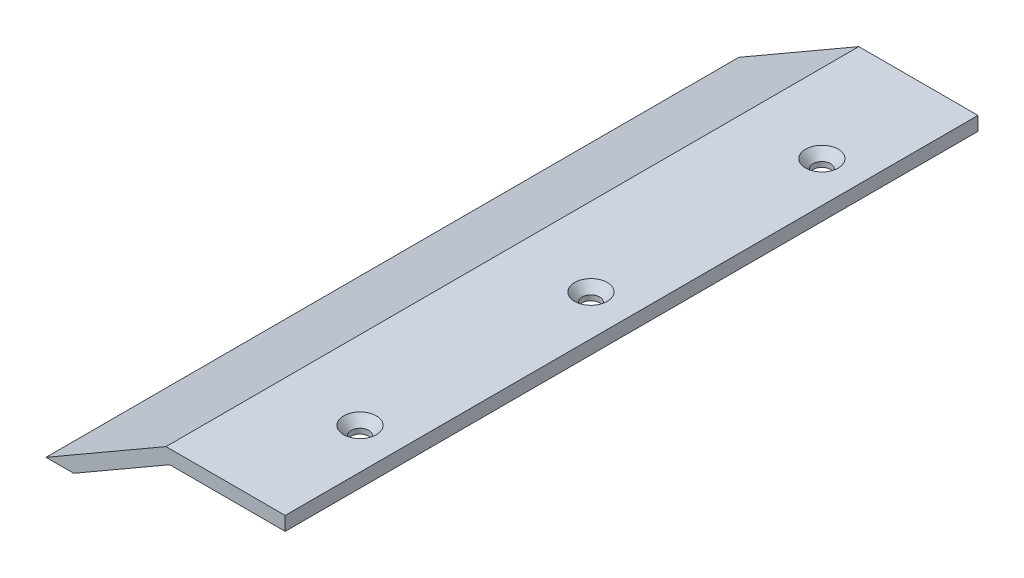
SolidWorks part; units mm, degrees
ref_plane "Alzado" through (0, 0, 0) normal (0, 0, 1) x (1, 0, 0)
ref_plane "Planta" through (0, 0, 0) normal (0, 1, 0) x (1, 0, 0)
ref_plane "Vista lateral" through (0, 0, 0) normal (1, 0, 0) x (0, 0, -1)
sketch "Croquis1" plane through (0, 0, 0) normal (0, 0, 1) x (1, 0, 0)
  line L1 (25, 0) -> (25, 3)
  line L2 (25, 3) -> (-0.8038, 3)
  line L3 (-0.8038, 3) -> (-26.7846, -12)
  line L4 (-26.7846, -12) -> (-20.7846, -12)
  line L5 (-20.7846, -12) -> (0, 0)
  line L7 (25, 0) -> (0, 0)
  line L8 (3.8354, 2.2216) -> (3.8354, -24.8486) construction
  dimension "D1" = 3
  dimension "D2" = 3
  dimension "D3" = 30
  dimension "D4" = 30.62
  dimension "D5" = 15
  dimension "D6" = 25
extrude "Saliente-Extruir1" add sketch "Croquis1" along normal mid plane 150
sketch "Croquis3" plane through (0, 3, 0) normal (0, 1, 0) x (1, 0, 0)
  line L0 (-61.5201, 0) -> (49.3842, 0) construction
  line L2 (16.2, 0) -> (16.2, 50) construction
  line L3 (16.2, 0) -> (16.2, -50) construction
  line L4 (25, -75) -> (25, 75) construction
  circle A0 centre (16.2, 0) radius 1.9844
  circle A1 centre (16.2, 50) radius 1.9844
  circle A2 centre (16.2, -50) radius 1.9844
  dimension "D1" = 3.9688
  dimension "D2" = 8.8
  dimension "D4" = 50
  dimension "D6" = 50
  dimension "D3" = 2
  dimension "D5" = 2
hole_wizard "Avellanado para tornillo con cabeza ovalada de #61" positions "Croquis3D3" profile "Croquis4" countersink size "#6" standard "Ansi Inch"
sketch3d "Croquis3D3"
  point P0 (16.2, 3, -50)
  point P3 (16.2, 3, 0)
  point P6 (16.2, 3, 50)
sketch "Croquis4" plane through (16.2, 3, -50) normal (1, 0, 0) x (0, 0, 1)
  line L0 (0, 0) -> (0, 21.1408)
  line L1 (0, 21.1408) -> (1.8986, 20)
  line L2 (1.8986, 20) -> (1.8986, 1.892)
  line L3 (1.8986, 1.892) -> (3.5433, 0)
  line L5 (3.5433, 0) -> (0, 0)
  line L6 (-1.8986, 1.892) -> (-3.5433, 0) construction
  line L10 (0, 21.1408) -> (-1.8987, 20) construction
  line L11 (0, -6.35) -> (0, 107.95) construction
  dimension "Diámetro de taladro" = 3.7973
  dimension "Profundidad de taladro" = 20
  dimension "Ángulo de avellanado cercano" = 7.0866
  dimension "Ángulo de avellanado lejano" = 82
  dimension "Ángulo de perforador" = 118
